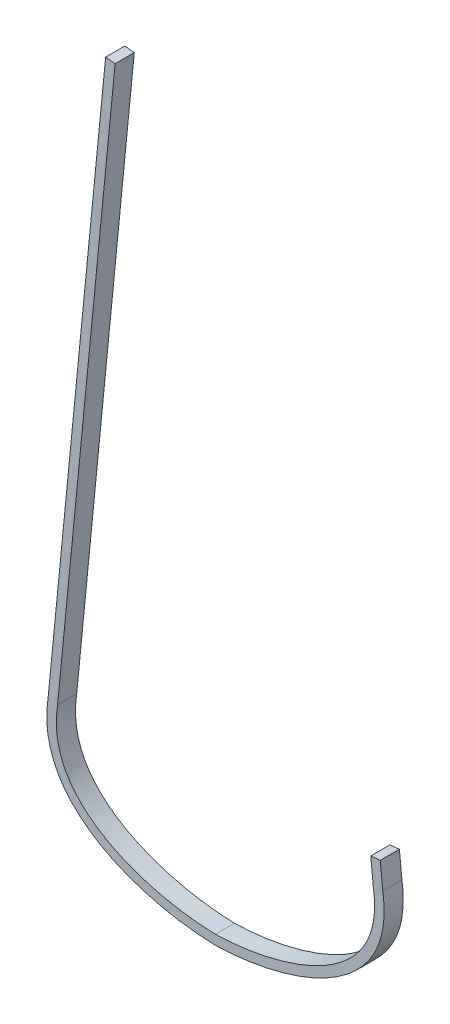
SolidWorks part; units mm, degrees
ref_plane "Front Plane" through (0, 0, 0) normal (0, 0, 1) x (1, 0, 0)
ref_plane "Top Plane" through (0, 0, 0) normal (0, 1, 0) x (1, 0, 0)
ref_plane "Right Plane" through (0, 0, 0) normal (1, 0, 0) x (0, 0, -1)
sketch "Sketch1" plane through (0, 0, 0) normal (0, 0, 1) x (1, 0, 0)
  line L0 (157.2341, 128.9805) -> (154.7163, 154.5179)
  line L1 (-157.2341, 128.9805) -> (-99.8892, 710.6217)
  line L2 (-109.3682, 711.5562) -> (-99.8892, 710.6217)
  line L3 (154.7163, 154.5179) -> (164.1954, 155.4524)
  line L4 (166.6875, 130.175) -> (106.8761, 736.8337) construction
  line L5 (157.2341, 128.9805) -> (97.8226, 731.5828) construction
  line L6 (-166.6875, 130.175) -> (-109.3682, 711.5562)
  line L7 (166.6875, 130.175) -> (164.1954, 155.4524)
  line L8 (106.8761, 736.8337) -> (0, 812.8) construction
  line L9 (97.8226, 731.5828) -> (0, 801.114) construction
  line L10 (-106.8761, 736.8337) -> (0, 812.8) construction
  line L11 (-97.8226, 731.5828) -> (0, 801.114) construction
  line L12 (-157.2341, 128.9805) -> (-97.8226, 731.5828) construction
  line L13 (-166.6875, 130.175) -> (-106.8761, 736.8337) construction
  spline S0 degree 3 poles (0, 0) (-73.6666, 1.7407) (-181.1881, 36.2008) (-166.6875, 130.175) knots 0 0 0 0 1 1 1 1
  spline S2 degree 3 poles (0, 0) (73.6666, 1.7407) (181.1881, 36.2008) (166.6875, 130.175) knots 0 0 0 0 1 1 1 1
  spline S6 degree 1 poles (0, 9.5278) (157.2341, 128.9805) knots 0 0 1 1 construction
  spline S7 degree 1 poles (0, 9.5278) (-157.2341, 128.9805) knots 0 0 1 1 construction
  spline S10 degree 3 poles (157.2341, 128.9805) (157.2612, 128.8048) (157.3166, 128.4467) (157.4158, 127.7819) (157.5841, 126.6011) (157.8817, 124.2773) (158.2064, 121.0104) (158.4372, 117.1902) (158.5402, 112.2214) (158.2964, 106.2423) (157.4427, 99.4182) (156.0586, 92.9236) (153.5414, 84.674) (149.1923, 75.0755) (142.1891, 64.5645) (130.6439, 51.8036) (112.4361, 38.1575) (90.5159, 27.6265) (71.6896, 21.0509) (57.1652, 17.0231) (42.4775, 13.8759) (30.3032, 11.9623) (20.7255, 10.8404) (13.6522, 10.199) (7.88, 9.8272) (3.3405, 9.6248) (1.1176, 9.5552) (0, 9.5278) knots 0.001057 0.001057 0.001057 0.001057 0.00301 0.004963 0.008868 0.01668 0.032303 0.047925 0.063548 0.094794 0.126039 0.157285 0.188531 0.251022 0.313513 0.376004 0.500986 0.625969 0.68846 0.750951 0.813442 0.875933 0.907179 0.938424 0.96967 0.985293 1.000916 1.000916 1.000916 1.000916
  spline S11 degree 3 poles (0, 9.5278) (-1.1176, 9.5552) (-3.3405, 9.6248) (-7.88, 9.8272) (-13.6522, 10.199) (-20.7255, 10.8404) (-30.3032, 11.9623) (-42.4775, 13.8759) (-57.1652, 17.0231) (-71.6896, 21.0509) (-90.5159, 27.6265) (-112.4361, 38.1575) (-130.6439, 51.8036) (-142.1891, 64.5645) (-149.1923, 75.0755) (-153.5414, 84.674) (-156.0586, 92.9236) (-157.4427, 99.4182) (-158.2964, 106.2423) (-158.5402, 112.2214) (-158.4372, 117.1902) (-158.2064, 121.0104) (-157.8817, 124.2773) (-157.5841, 126.6011) (-157.4158, 127.7819) (-157.3166, 128.4467) (-157.2612, 128.8048) (-157.2341, 128.9805) knots 0.001057 0.001057 0.001057 0.001057 0.01668 0.032303 0.063548 0.094794 0.126039 0.188531 0.251022 0.313513 0.376004 0.500986 0.625969 0.68846 0.750951 0.813442 0.844688 0.875933 0.907179 0.938424 0.954047 0.96967 0.985293 0.993104 0.99701 0.998963 1.000916 1.000916 1.000916 1.000916
  dimension "D2" = 333.375
  dimension "D3" = 9.525
  dimension "D5" = 25.4
extrude "Boss-Extrude1" add sketch "Sketch1" along normal blind 19.05
